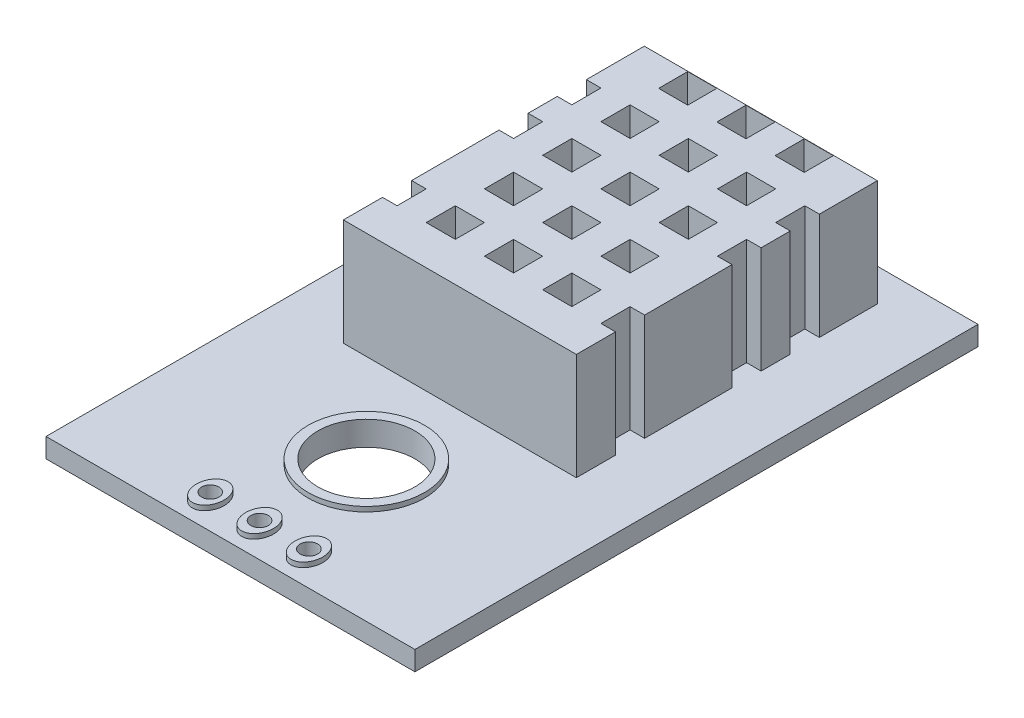
SolidWorks part; units mm, degrees
ref_plane "Front Plane" through (0, 0, 0) normal (0, 0, 1) x (1, 0, 0)
ref_plane "Top Plane" through (0, 0, 0) normal (0, 1, 0) x (1, 0, 0)
ref_plane "Right Plane" through (0, 0, 0) normal (1, 0, 0) x (0, 0, -1)
sketch "Sketch1" plane through (0, 0, 0) normal (0, 1, 0) x (1, 0, 0)
  line L0 (0, 23.0065) -> (0, -23.0065) construction
  line L1 (-9.5, 14.5) -> (9.5, 14.5)
  line L2 (-9.5, 14.5) -> (-9.5, -14.5)
  line L3 (-9.5, -14.5) -> (9.5, -14.5)
  line L4 (9.5, 14.5) -> (9.5, -14.5)
  line L5 (-9.5, 14.5) -> (9.5, -14.5) construction
  line L6 (-9.5, -14.5) -> (9.5, 14.5) construction
  circle A3 centre (0, -7.5) radius 2.5
  point P0 (0, 0)
  point P9 (0, 0)
  dimension "D3" = 5
  dimension "D4" = 7
  dimension "D1" = 19
  dimension "D2" = 29
extrude "Boss-Extrude2" add sketch "Sketch1" against normal blind 1 contours L2 L3 L4 L1 | A3
sketch "Sketch3" plane through (0, 0, 0) normal (0, 1, 0) x (1, 0, 0)
  line L0 (0, 19.1879) -> (0, -34.1879) construction
  line L1 (-9.5, -14.5) -> (9.5, -14.5) construction
  circle A0 centre (0, -13) radius 0.45
  circle A1 centre (2.54, -13) radius 0.45
  circle A2 centre (-2.54, -13) radius 0.45
  circle A3 centre (0, -7.5) radius 2.5
  circle A4 centre (0, -7.5) radius 3
  ellipse E0 centre (0, -13) end of major axis (0, -13.9221) minor radius 0.7135
  ellipse E1 centre (2.54, -13) end of major axis (2.54, -13.9221) minor radius 0.7135
  ellipse E2 centre (-2.54, -13) end of major axis (-2.54, -13.9221) minor radius 0.7135
  point P5 (0, -7.5)
  dimension "D1" = 0.9
  dimension "D2" = 0.9
  dimension "D6" = 5
  dimension "D7" = 6
  dimension "D3" = 1.5
  dimension "D4" = 1.5
  dimension "D5" = 2.54
extrude "Boss-Extrude3" add sketch "Sketch3" along normal blind 0.25
sketch "Sketch4" plane through (0, 0, 0) normal (0, 1, 0) x (1, 0, 0)
  circle A0 centre (-2.54, -13) radius 0.45
  circle A1 centre (0, -13) radius 0.45
  circle A2 centre (2.54, -13) radius 0.45
extrude "Cut-Extrude1" cut sketch "Sketch4" against normal blind 2 and the other way through all
sketch "Sketch5" plane through (0, 0, 0) normal (0, 1, 0) x (1, 0, 0)
  line L0 (0, 25.9322) -> (0, -25.9322) construction
  line L2 (-6, 12.8156) -> (6, 12.8156)
  line L3 (-6, 12.8156) -> (-6, -2.6844)
  line L4 (-6, -2.6844) -> (6, -2.6844)
  line L5 (6, 12.8156) -> (6, -2.6844)
  line L6 (-6, 12.8156) -> (6, -2.6844) construction
  line L7 (-6, -2.6844) -> (6, 12.8156) construction
  point P0 (0, 5.0656)
  point P4 (0, 0)
  dimension "D1" = 12
  dimension "D2" = 15.5
extrude "Boss-Extrude4" add sketch "Sketch5" along normal blind 5.5
sketch "Sketch7" plane through (0, 0, 0) normal (0, 1, 0) x (1, 0, 0)
  line L0 (0, 25.4093) -> (0, -25.4093) construction
  line L1 (-3.75, 12.8009) -> (-3.75, 11.3009)
  line L2 (-0.75, 12.8009) -> (0.75, 12.8009)
  line L3 (-0.75, 12.8009) -> (-0.75, 11.3009)
  line L4 (-0.75, 11.3009) -> (0.75, 11.3009)
  line L5 (0.75, 12.8009) -> (0.75, 11.3009)
  line L6 (-0.75, 12.8009) -> (0.75, 11.3009) construction
  line L7 (-0.75, 11.3009) -> (0.75, 12.8009) construction
  line L8 (2.25, 12.8009) -> (3.75, 12.8009)
  line L9 (2.25, 12.8009) -> (2.25, 11.3009)
  line L10 (2.25, 11.3009) -> (3.75, 11.3009)
  line L11 (3.75, 12.8009) -> (3.75, 11.3009)
  line L12 (2.25, 12.8009) -> (3.75, 11.3009) construction
  line L13 (2.25, 11.3009) -> (3.75, 12.8009) construction
  line L14 (-2.25, 12.8009) -> (-3.75, 12.8009)
  line L15 (-2.25, 12.8009) -> (-2.25, 11.3009)
  line L16 (-2.25, 11.3009) -> (-3.75, 11.3009)
  line L17 (-15.2954, 10.5656) -> (15.2954, 10.5656) construction
  line L18 (6, 12.8156) -> (-6, 12.8156) construction
  line L19 (2.25, 9.8303) -> (3.75, 8.3303) construction
  line L20 (2.25, 8.3303) -> (3.75, 9.8303) construction
  line L21 (-0.75, 9.8303) -> (0.75, 8.3303) construction
  line L22 (-0.75, 8.3303) -> (0.75, 9.8303) construction
  line L23 (-2.25, 9.8303) -> (-3.75, 9.8303)
  line L24 (-2.25, 8.3303) -> (-2.25, 9.8303)
  line L25 (-2.25, 8.3303) -> (-3.75, 8.3303)
  line L26 (3.75, 8.3303) -> (3.75, 9.8303)
  line L27 (2.25, 9.8303) -> (3.75, 9.8303)
  line L28 (2.25, 8.3303) -> (2.25, 9.8303)
  line L29 (2.25, 8.3303) -> (3.75, 8.3303)
  line L30 (0.75, 8.3303) -> (0.75, 9.8303)
  line L31 (-0.75, 9.8303) -> (0.75, 9.8303)
  line L32 (-0.75, 8.3303) -> (-0.75, 9.8303)
  line L33 (-0.75, 8.3303) -> (0.75, 8.3303)
  line L34 (-3.75, 8.3303) -> (-3.75, 9.8303)
  line L35 (-17.4084, 7.5803) -> (17.4084, 7.5803) construction
  line L36 (-0.75, 6.8303) -> (0.75, 5.3303) construction
  line L37 (-0.75, 5.3303) -> (0.75, 6.8303) construction
  line L38 (2.25, 6.8303) -> (3.75, 5.3303) construction
  line L39 (2.25, 5.3303) -> (3.75, 6.8303) construction
  line L40 (-3.75, 6.8303) -> (-3.75, 5.3303)
  line L41 (-0.75, 6.8303) -> (0.75, 6.8303)
  line L42 (-0.75, 6.8303) -> (-0.75, 5.3303)
  line L43 (-0.75, 5.3303) -> (0.75, 5.3303)
  line L44 (0.75, 6.8303) -> (0.75, 5.3303)
  line L45 (2.25, 6.8303) -> (3.75, 6.8303)
  line L46 (2.25, 6.8303) -> (2.25, 5.3303)
  line L47 (2.25, 5.3303) -> (3.75, 5.3303)
  line L48 (3.75, 6.8303) -> (3.75, 5.3303)
  line L49 (-2.25, 6.8303) -> (-3.75, 6.8303)
  line L50 (-2.25, 6.8303) -> (-2.25, 5.3303)
  line L51 (-2.25, 5.3303) -> (-3.75, 5.3303)
  line L52 (-17.4084, 4.5803) -> (17.4084, 4.5803) construction
  line L53 (2.25, 3.8303) -> (3.75, 2.3303) construction
  line L54 (2.25, 2.3303) -> (3.75, 3.8303) construction
  line L55 (-0.75, 3.8303) -> (0.75, 2.3303) construction
  line L56 (-0.75, 2.3303) -> (0.75, 3.8303) construction
  line L57 (-2.25, 3.8303) -> (-3.75, 3.8303)
  line L58 (-2.25, 2.3303) -> (-2.25, 3.8303)
  line L59 (-2.25, 2.3303) -> (-3.75, 2.3303)
  line L60 (3.75, 2.3303) -> (3.75, 3.8303)
  line L61 (2.25, 3.8303) -> (3.75, 3.8303)
  line L62 (2.25, 2.3303) -> (2.25, 3.8303)
  line L63 (2.25, 2.3303) -> (3.75, 2.3303)
  line L64 (0.75, 2.3303) -> (0.75, 3.8303)
  line L65 (-0.75, 3.8303) -> (0.75, 3.8303)
  line L66 (-0.75, 2.3303) -> (-0.75, 3.8303)
  line L67 (-0.75, 2.3303) -> (0.75, 2.3303)
  line L68 (-3.75, 2.3303) -> (-3.75, 3.8303)
  line L69 (-17.1273, 1.5803) -> (17.1273, 1.5803) construction
  line L70 (-0.75, 0.8303) -> (0.75, -0.6697) construction
  line L71 (-0.75, -0.6697) -> (0.75, 0.8303) construction
  line L72 (2.25, 0.8303) -> (3.75, -0.6697) construction
  line L73 (2.25, -0.6697) -> (3.75, 0.8303) construction
  line L74 (-3.75, 0.8303) -> (-3.75, -0.6697)
  line L75 (-0.75, 0.8303) -> (0.75, 0.8303)
  line L76 (-0.75, 0.8303) -> (-0.75, -0.6697)
  line L77 (-0.75, -0.6697) -> (0.75, -0.6697)
  line L78 (0.75, 0.8303) -> (0.75, -0.6697)
  line L79 (2.25, 0.8303) -> (3.75, 0.8303)
  line L80 (2.25, 0.8303) -> (2.25, -0.6697)
  line L81 (2.25, -0.6697) -> (3.75, -0.6697)
  line L82 (3.75, 0.8303) -> (3.75, -0.6697)
  line L83 (-2.25, 0.8303) -> (-3.75, 0.8303)
  line L84 (-2.25, 0.8303) -> (-2.25, -0.6697)
  line L85 (-2.25, -0.6697) -> (-3.75, -0.6697)
  line L86 (6, -2.6844) -> (6, 12.8156) construction
  line L87 (5.25, 6.8303) -> (6, 6.8303)
  line L88 (5.25, 6.8303) -> (5.25, 5.3303)
  line L89 (5.25, 5.3303) -> (6, 5.3303)
  line L90 (6, 6.8303) -> (6, 5.3303)
  line L91 (5.25, 6.8303) -> (6, 5.3303) construction
  line L92 (5.25, 5.3303) -> (6, 6.8303) construction
  line L93 (-5.25, 5.3303) -> (-6, 6.8303) construction
  line L94 (-5.25, 6.8303) -> (-6, 5.3303) construction
  line L95 (-6, 6.8303) -> (-6, 5.3303)
  line L96 (-5.25, 5.3303) -> (-6, 5.3303)
  line L97 (-5.25, 6.8303) -> (-5.25, 5.3303)
  line L98 (-5.25, 6.8303) -> (-6, 6.8303)
  line L99 (5.25, 9.8303) -> (6, 8.3303) construction
  line L100 (5.25, 8.3303) -> (6, 9.8303) construction
  line L101 (6, 8.3303) -> (6, 9.8303)
  line L102 (5.25, 9.8303) -> (6, 9.8303)
  line L103 (5.25, 8.3303) -> (5.25, 9.8303)
  line L104 (5.25, 8.3303) -> (6, 8.3303)
  line L105 (-5.25, 8.3303) -> (-6, 9.8303) construction
  line L106 (-5.25, 9.8303) -> (-6, 8.3303) construction
  line L107 (-5.25, 8.3303) -> (-6, 8.3303)
  line L108 (-5.25, 8.3303) -> (-5.25, 9.8303)
  line L109 (-5.25, 9.8303) -> (-6, 9.8303)
  line L110 (-6, 8.3303) -> (-6, 9.8303)
  line L111 (-5.25, -0.6697) -> (-6, 0.8303) construction
  line L112 (5.25, 0.8303) -> (6, 0.8303)
  line L113 (5.25, 0.8303) -> (5.25, -0.6697)
  line L114 (5.25, -0.6697) -> (6, -0.6697)
  line L115 (6, 0.8303) -> (6, -0.6697)
  line L116 (5.25, 0.8303) -> (6, -0.6697) construction
  line L117 (5.25, -0.6697) -> (6, 0.8303) construction
  line L118 (-5.25, 0.8303) -> (-6, -0.6697) construction
  line L119 (-6, 0.8303) -> (-6, -0.6697)
  line L120 (-5.25, -0.6697) -> (-6, -0.6697)
  line L121 (-5.25, 0.8303) -> (-5.25, -0.6697)
  line L122 (-5.25, 0.8303) -> (-6, 0.8303)
  point P0 (0, 12.0509)
  point P3 (3, 12.0509)
  point P5 (0, 0)
  point P22 (0, 10.5656)
  point P36 (3, 9.0803)
  point P37 (0, 9.0803)
  point P41 (0, 7.5803)
  point P53 (0, 6.0803)
  point P54 (3, 6.0803)
  point P58 (0, 4.5803)
  point P70 (3, 3.0803)
  point P71 (0, 3.0803)
  point P75 (0, 1.5803)
  point P87 (0, 0.0803)
  point P88 (3, 0.0803)
  point P89 (5.625, 6.0803)
  point P100 (-5.625, 6.0803)
  point P105 (5.625, 9.0803)
  point P110 (-5.625, 9.0803)
  point P111 (5.625, 0.0803)
  point P120 (-5.625, 0.0803)
  dimension "D1" = 1.5
  dimension "D2" = 1.5
  dimension "D3" = 1.5
  dimension "D4" = 3
  dimension "D5" = 2.25
  dimension "D6" = 2.25
  dimension "D7" = 2.25
  dimension "D8" = 2.25
  dimension "D9" = 0.75
  dimension "D10" = 1.5
extrude "Cut-Extrude2" cut sketch "Sketch7" along normal blind 6
